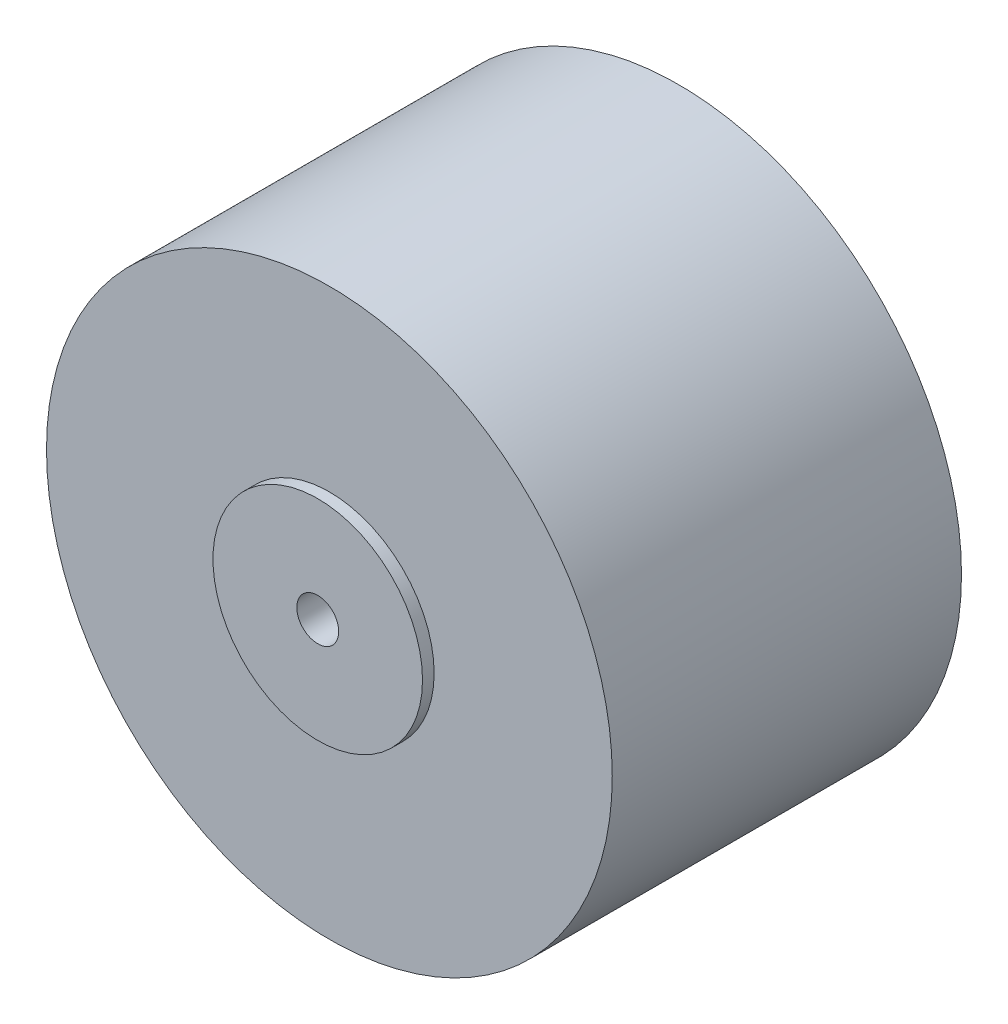
SolidWorks part; units mm, degrees
ref_plane "Plano frontal" through (0, 0, 0) normal (0, 0, 1) x (1, 0, 0)
ref_plane "Plano superior" through (0, 0, 0) normal (0, 1, 0) x (1, 0, 0)
ref_plane "Plano direito" through (0, 0, 0) normal (1, 0, 0) x (0, 0, -1)
sketch "Esboço1" plane through (0, 0, 0) normal (0, 0, 1) x (1, 0, 0)
  circle A0 centre (0, 0) radius 12.15
  dimension "D1" = 24.3
extrude "Ressalto-extrusão1" add sketch "Esboço1" along normal blind 15
sketch "Esboço2" plane through (0, 0, 0) normal (0, 0, 1) x (1, 0, 0)
  line L0 (-12.15, 0) -> (12.15, 0) construction
  line L1 (12.15, 0) -> (0, 12.15) construction
  line L2 (0, 12.15) -> (0, -12.15) construction
  circle A0 centre (0, 0) radius 12.15 construction
  circle A1 centre (0, 0) radius 4.5
  dimension "D1" = 9
extrude "Ressalto-extrusão2" add sketch "Esboço2" along normal blind 15.5
sketch "Esboço3" plane through (0, 0, 0) normal (0, 0, 1) x (1, 0, 0)
  circle A0 centre (0, 0) radius 0.9
  dimension "D1" = 1.8
extrude "Corte-extrusão1" cut sketch "Esboço3" against normal blind 15.5 and the other way blind 19.5
